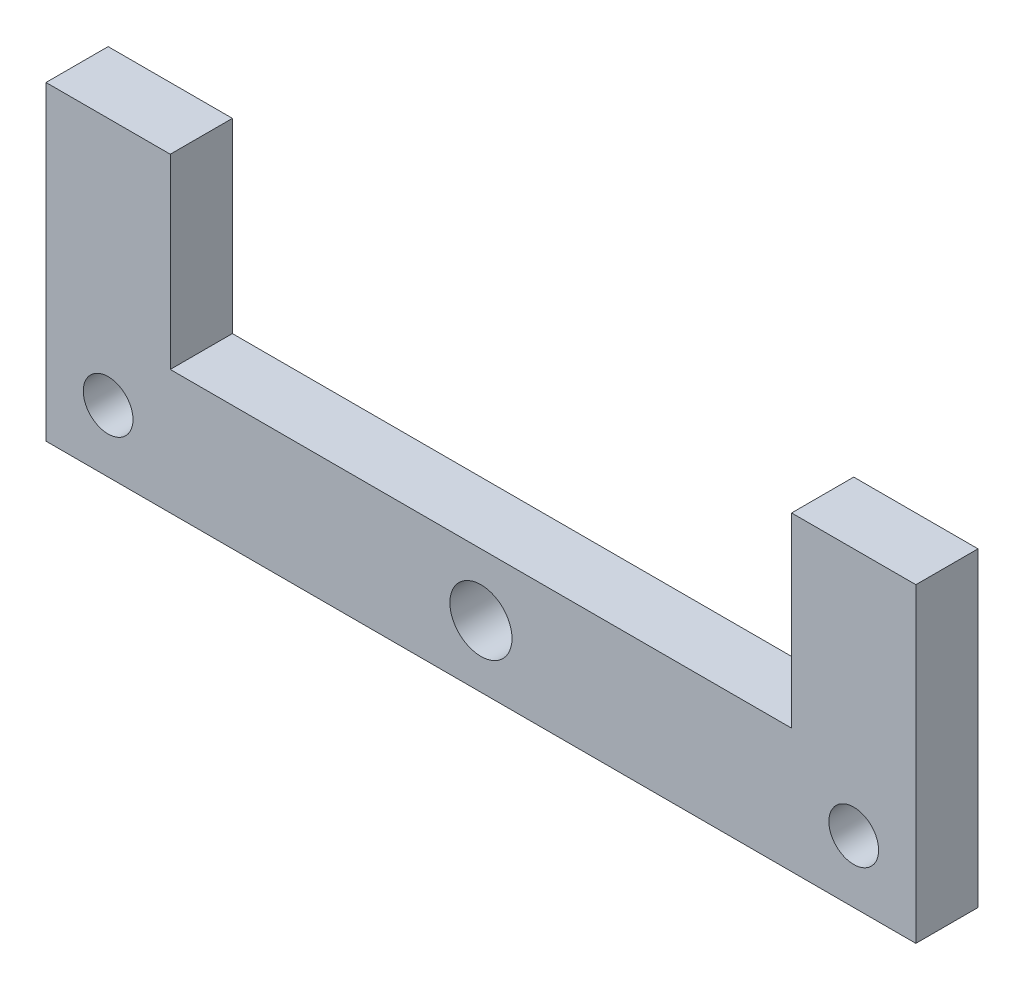
SolidWorks part; units mm, degrees
ref_plane "Plan de face" through (0, 0, 0) normal (0, 0, 1) x (1, 0, 0)
ref_plane "Plan de dessus" through (0, 0, 0) normal (0, 1, 0) x (1, 0, 0)
ref_plane "Plan de droite" through (0, 0, 0) normal (1, 0, 0) x (0, 0, -1)
sketch "Esquisse1" plane through (0, 0, 0) normal (0, 0, 1) x (1, 0, 0)
  line L0 (0, 0) -> (39.165, 0) construction
  line L1 (39.165, 0) -> (-46.8232, 0) construction
  line L2 (0, 0) -> (0, 19.9885) construction
  line L3 (-50, 10) -> (50, 10)
  line L4 (-70, 10) -> (-70, -10)
  line L5 (-70, -10) -> (70, -10)
  line L6 (70, 10) -> (70, -10)
  line L12 (-70, -10) -> (70, -10)
  line L14 (-70, 10) -> (-70, 40)
  line L15 (-70, 40) -> (-50, 40)
  line L16 (-50, 10) -> (-50, 40)
  line L18 (70, 10) -> (70, 40)
  line L19 (70, 40) -> (50, 40)
  line L20 (50, 10) -> (50, 40)
  circle A0 centre (0, 0) radius 5
  circle A1 centre (-60, 0) radius 4
  circle A2 centre (60, 0) radius 4
  dimension "D1" = 10
  dimension "D2" = 8
  dimension "D3" = 8
  dimension "D4" = 60
  dimension "D5" = 60
  dimension "D6" = 20
  dimension "D7" = 10
  dimension "D8" = 30
  dimension "D10" = 20
  dimension "D11" = 20
extrude "Boss.-Extru.1" add sketch "Esquisse1" along normal blind 10
